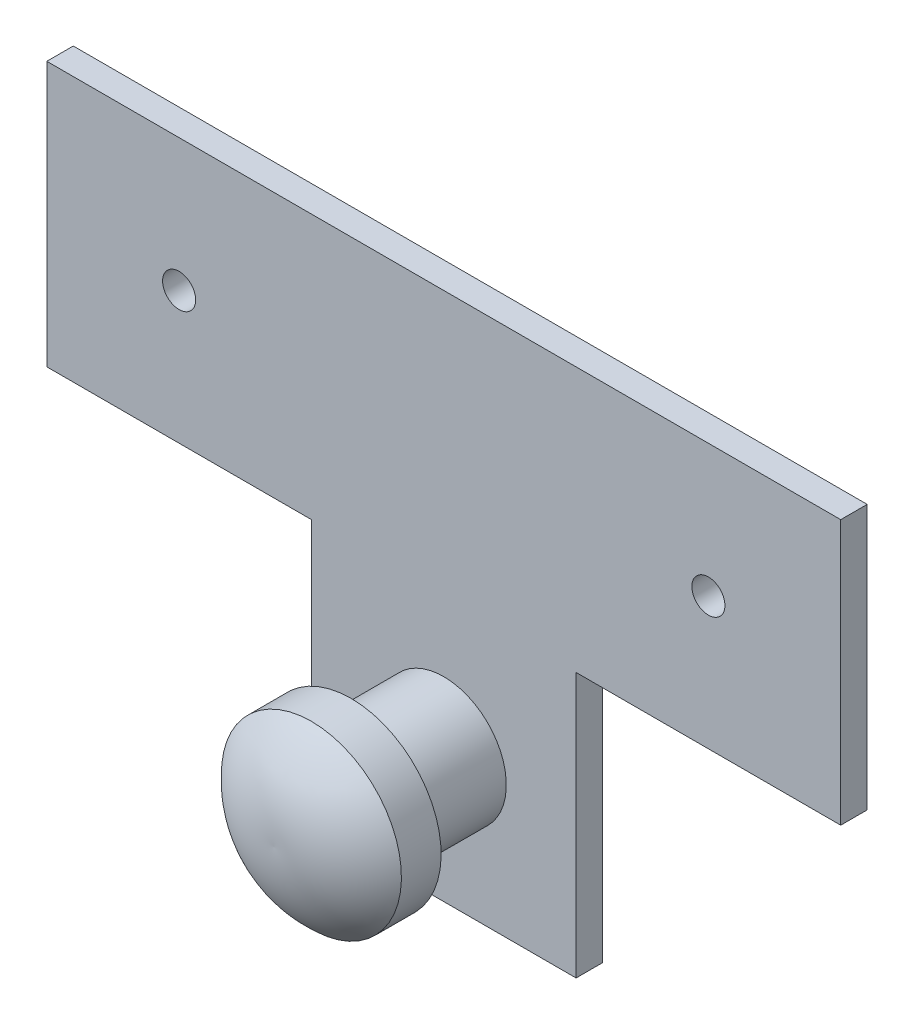
SolidWorks part; units mm, degrees
ref_plane "Front Plane" through (0, 0, 0) normal (0, 0, 1) x (1, 0, 0)
ref_plane "Top Plane" through (0, 0, 0) normal (0, 1, 0) x (1, 0, 0)
ref_plane "Right Plane" through (0, 0, 0) normal (1, 0, 0) x (0, 0, -1)
sketch "Sketch1" plane through (0, 0, 0) normal (0, 0, 1) x (1, 0, 0)
  line L0 (12.7, 0) -> (38.1, 0)
  line L14 (-12.7, 0) -> (-12.7, -25.4)
  line L15 (-12.7, -25.4) -> (12.7, -25.4)
  line L16 (12.7, 0) -> (12.7, -25.4)
  line L17 (-38.1, 25.4) -> (38.1, 25.4)
  line L18 (-38.1, 25.4) -> (-38.1, 0)
  line L19 (-38.1, 0) -> (-12.7, 0)
  line L20 (38.1, 25.4) -> (38.1, 0)
  point P8 (0, -25.4)
  point P10 (0, 25.4)
  point P11 (0, 0)
  point P12 (0, 0)
  dimension "D1" = 76.2
  dimension "D2" = 50.8
  dimension "D3" = 25.4
  dimension "D4" = 25.4
extrude "Boss-Extrude1" add sketch "Sketch1" along normal blind 2.54
sketch "Sketch2" plane through (0, 0, 2.54) normal (0, 0, 1) x (1, 0, 0)
  line L0 (-12.7, 0) -> (12.7, -25.4) construction
  line L1 (12.7, 0) -> (-12.7, -25.4) construction
  line L2 (12.7, 0) -> (38.1, 0) construction
  circle A0 centre (0, -12.7) radius 6
  dimension "D1" = 12
extrude "Boss-Extrude2" add sketch "Sketch2" along normal blind 8.89
sketch "Sketch4" plane through (0, 0, 0) normal (1, 0, 0) x (0, 0, -1)
  line L0 (-11.43, -6.7) -> (-11.43, -18.7) construction
  line L1 (-11.43, -12.7) -> (-18.8545, -12.7)
  line L2 (-11.43, -12.7) -> (-11.43, -21.336)
  line L3 (-11.43, -21.336) -> (-15.24, -21.336)
  arc A0 (-15.24, -21.336) -> (-18.8545, -12.7) centre (-8.1956, -13.3132) cw
  point P4 (0, 0)
  point P10 (-11.43, -21.7989)
  dimension "D2" = 10.6765
  dimension "D1" = 3.81
  dimension "D3" = 8.636
  dimension "D4" = 7.4245
revolve "Revolve1" add sketch "Sketch4" angle 360 about L1
sketch "Sketch5" plane through (0, 0, 0) normal (0, 0, -1) x (-1, 0, 0)
  line L0 (38.1, 25.4) -> (12.7, 0) construction
  line L1 (-38.1, 25.4) -> (-12.7, 0) construction
  circle A0 centre (25.4, 12.7) radius 1.5875
  circle A1 centre (-25.4, 12.7) radius 1.5875
  dimension "D1" = 3.175
extrude "Cut-Extrude1" cut sketch "Sketch5" against normal up to next
